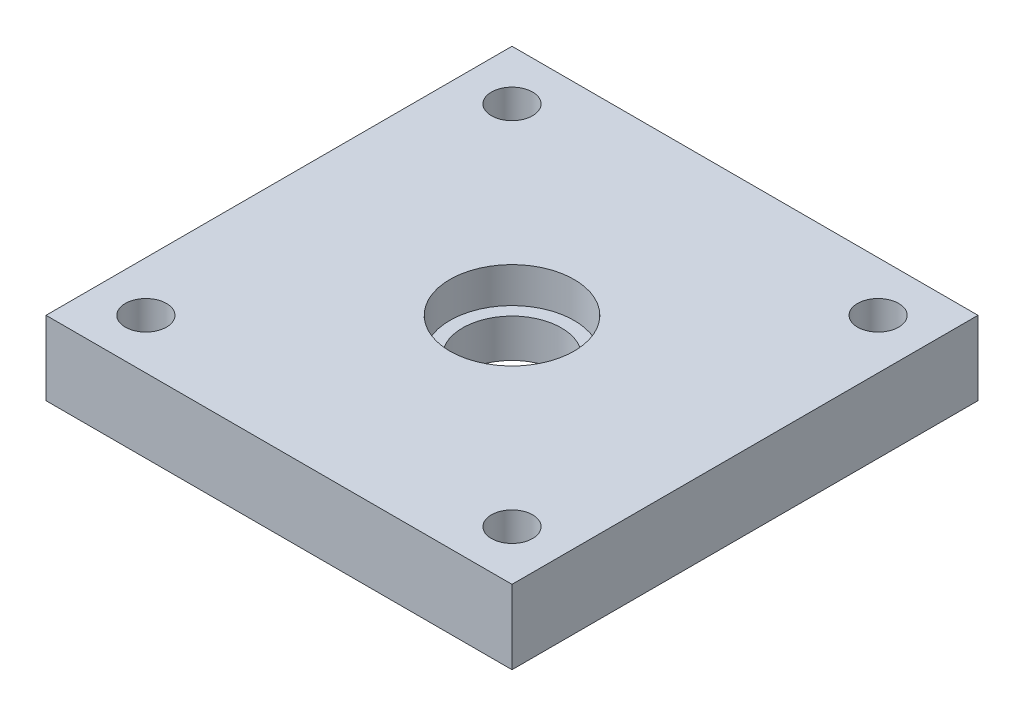
SolidWorks part; units mm, degrees
ref_plane "Front Plane" through (0, 0, 0) normal (0, 0, 1) x (1, 0, 0)
ref_plane "Top Plane" through (0, 0, 0) normal (0, 1, 0) x (1, 0, 0)
ref_plane "Right Plane" through (0, 0, 0) normal (1, 0, 0) x (0, 0, -1)
sketch "Sketch1" plane through (0, 0, 0) normal (0, 1, 0) x (1, 0, 0)
  line L1 (-30, 30) -> (30, 30)
  line L2 (-30, 30) -> (-30, -30)
  line L3 (-30, -30) -> (30, -30)
  line L4 (30, 30) -> (30, -30)
  line L5 (-30, 30) -> (30, -30) construction
  line L6 (-30, -30) -> (30, 30) construction
  point P0 (0, 0)
  dimension "D1" = 60
  dimension "D2" = 60
extrude "Boss-Extrude1" add sketch "Sketch1" along normal blind 9.525
hole_wizard "M5 Clearance Hole1" positions "Sketch3" profile "Sketch2" hole size "M5" standard "ANSI Metric" end condition through all
sketch "Sketch3" plane through (0, 9.525, 0) normal (0, 1, 0) x (1, 0, 0)
  point P0 (-23.57, 23.57)
  point P2 (23.57, 23.57)
  point P4 (23.57, -23.57)
  point P6 (-23.57, -23.57)
  dimension "D1" = 47.14
  dimension "D2" = 47.14
  dimension "D3" = 23.57
  dimension "D4" = 23.57
sketch "Sketch2" plane through (-23.57, 9.525, -23.57) normal (1, 0, 0) x (0, 0, 1)
  line L0 (0, 0) -> (0, 9.525)
  line L1 (0, 9.525) -> (2.65, 9.525)
  line L2 (2.65, 9.525) -> (2.65, 0)
  line L5 (2.65, 0) -> (0, 0)
  line L11 (0, -6.35) -> (0, 107.95) construction
  dimension "Thru Hole Dia." = 5.3
  dimension "Thru Hole Depth" = 9.525
sketch "Sketch5" plane through (0, 9.525, 0) normal (0, 1, 0) x (1, 0, 0)
  circle A0 centre (0, 0) radius 8
  dimension "D1" = 16
extrude "Cut-Extrude1" cut sketch "Sketch5" against normal blind 4.572 contours A0
sketch "Sketch6" plane through (0, 4.953, 0) normal (0, 1, 0) x (1, 0, 0)
  circle A0 centre (0, 0) radius 6.35
  dimension "D1" = 12.7
extrude "Cut-Extrude2" cut sketch "Sketch6" against normal through all
